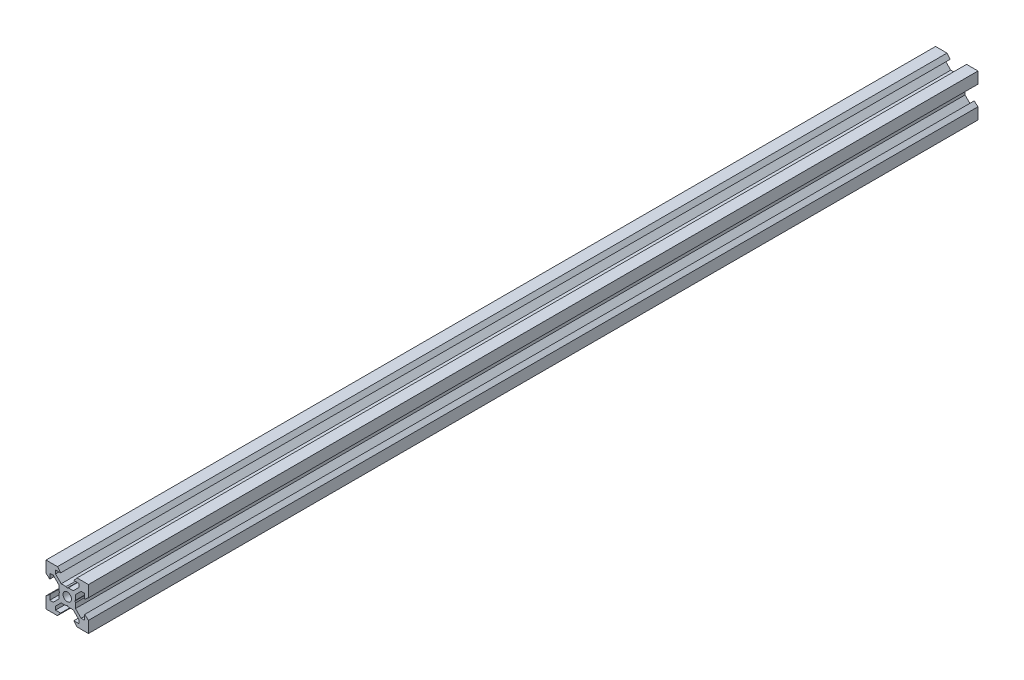
SolidWorks part; units mm, degrees
ref_plane "Front Plane" through (0, 0, 0) normal (0, 0, 1) x (1, 0, 0)
ref_plane "Top Plane" through (0, 0, 0) normal (0, 1, 0) x (1, 0, 0)
ref_plane "Right Plane" through (0, 0, 0) normal (1, 0, 0) x (0, 0, -1)
sketch "Sketch1" plane through (0, 0, 0) normal (0, 0, 1) x (1, 0, 0)
  line L0 (10, 10) -> (4.6104, 10) construction
  line L1 (10, 10) -> (10, 4.6104) construction
  line L2 (10, -10) -> (10, -4.6104) construction
  line L3 (10, -10) -> (4.6104, -10) construction
  line L4 (10, 10) -> (10, 4.6104)
  line L5 (6.5607, 5.5) -> (8.2, 5.5)
  line L6 (5.5, 8.2) -> (5.5, 6.5607)
  line L7 (10, 10) -> (4.6104, 10)
  line L8 (10, 10) -> (10, 4.6104)
  line L9 (6.5607, 5.5) -> (3.9, 2.8393)
  line L10 (5.5, 6.5607) -> (2.8393, 3.9)
  line L11 (10, 4.6104) -> (8.2, 3.1)
  line L12 (4.6104, 10) -> (3.1, 8.2)
  line L13 (8.2, 3.1) -> (8.2, 5.5)
  line L14 (3.1, 8.2) -> (5.5, 8.2)
  line L15 (-6.5607, 5.5) -> (-8.2, 5.5)
  line L16 (6.5607, -5.5) -> (8.2, -5.5)
  line L17 (3.1, -8.2) -> (5.5, -8.2)
  line L18 (8.2, -3.1) -> (8.2, -5.5)
  line L19 (4.6104, -10) -> (3.1, -8.2)
  line L20 (10, -4.6104) -> (8.2, -3.1)
  line L21 (0.5196, -3.9) -> (0, -3.6)
  line L22 (0.5196, 3.9) -> (0, 3.6)
  line L23 (3.6, 0) -> (3.9, -0.5196)
  line L24 (3.9, 0.5196) -> (3.6, 0)
  line L25 (3.9, 0.5196) -> (3.9, 2.8393)
  line L26 (2.8393, 3.9) -> (0.5196, 3.9)
  line L27 (3.9, -2.8393) -> (3.9, -0.5196)
  line L28 (2.8393, -3.9) -> (0.5196, -3.9)
  line L29 (5.5, -6.5607) -> (2.8393, -3.9)
  line L30 (6.5607, -5.5) -> (3.9, -2.8393)
  line L31 (10, -10) -> (10, -4.6104)
  line L32 (10, -10) -> (4.6104, -10)
  line L33 (5.5, -8.2) -> (5.5, -6.5607)
  line L34 (-6.5607, -5.5) -> (-8.2, -5.5)
  line L35 (10, -10) -> (10, -4.6104)
  line L36 (0, 0) -> (0, 8.2) construction
  line L37 (-10, -10) -> (-4.6104, -10) construction
  line L38 (-10, -10) -> (-10, -4.6104) construction
  line L39 (-10, 10) -> (-10, 4.6104) construction
  line L40 (-10, 10) -> (-4.6104, 10) construction
  line L41 (-10, -10) -> (-10, -4.6104)
  line L43 (-5.5, -8.2) -> (-5.5, -6.5607)
  line L44 (-10, -10) -> (-4.6104, -10)
  line L45 (-10, -10) -> (-10, -4.6104)
  line L46 (-6.5607, -5.5) -> (-3.9, -2.8393)
  line L47 (-5.5, -6.5607) -> (-2.8393, -3.9)
  line L48 (-2.8393, -3.9) -> (-0.5196, -3.9)
  line L49 (-3.9, -2.8393) -> (-3.9, -0.5196)
  line L50 (-2.8393, 3.9) -> (-0.5196, 3.9)
  line L51 (-3.9, 0.5196) -> (-3.9, 2.8393)
  line L52 (-3.9, 0.5196) -> (-3.6, 0)
  line L53 (-3.6, 0) -> (-3.9, -0.5196)
  line L54 (-0.5196, 3.9) -> (0, 3.6)
  line L55 (-0.5196, -3.9) -> (0, -3.6)
  line L56 (-10, -4.6104) -> (-8.2, -3.1)
  line L57 (-4.6104, -10) -> (-3.1, -8.2)
  line L58 (-8.2, -3.1) -> (-8.2, -5.5)
  line L59 (-3.1, -8.2) -> (-5.5, -8.2)
  line L60 (-10, -10) -> (10, -10) construction
  line L61 (-10, -10) -> (-10, 10) construction
  line L62 (-3.1, 8.2) -> (-5.5, 8.2)
  line L63 (-8.2, 3.1) -> (-8.2, 5.5)
  line L64 (-4.6104, 10) -> (-3.1, 8.2)
  line L65 (-10, 4.6104) -> (-8.2, 3.1)
  line L66 (-5.5, 6.5607) -> (-2.8393, 3.9)
  line L67 (-6.5607, 5.5) -> (-3.9, 2.8393)
  line L68 (-10, 10) -> (-10, 4.6104)
  line L69 (-10, 10) -> (-4.6104, 10)
  line L70 (-5.5, 8.2) -> (-5.5, 6.5607)
  line L71 (-10, 10) -> (10, 10) construction
  line L72 (-10, 10) -> (-10, 4.6104)
  line L73 (10, -10) -> (10, 10) construction
  line L74 (-10, -10) -> (10, 10) construction
  line L75 (-10, 10) -> (10, -10) construction
  circle A0 centre (0, 0) radius 2
  dimension "D7" = 4
  dimension "D1" = 20
  dimension "D2" = 5.3896
  dimension "D3" = 4.5
  dimension "D4" = 50
  dimension "D5" = 1.8
  dimension "D6" = 1.5104
  dimension "D8" = 5.5
  dimension "D9" = 120
  dimension "D10" = 0.3
  dimension "D11" = 2.3197
  dimension "D12" = 7.8
  dimension "D13" = 7.8
  dimension "D14" = 1.5
  dimension "D15" = 2.6607
extrude "Boss-Extrude1" add sketch "Sketch1" along normal mid plane 419.1 contours L70 L62 L64 L69 L68 L65 L63 L15 L67 L51 L52 L53 L49 L46 L34 L58 L56 L41 L44 L57 L59 L43 L47 L48 L55 L21 L28 L29 L33 L17 L19 L32 L31 L20 L18 L16 L30 L27 L23 L24 L25 L9 L5 L13 L11 L4 L7 L12 L14 L6 L10
